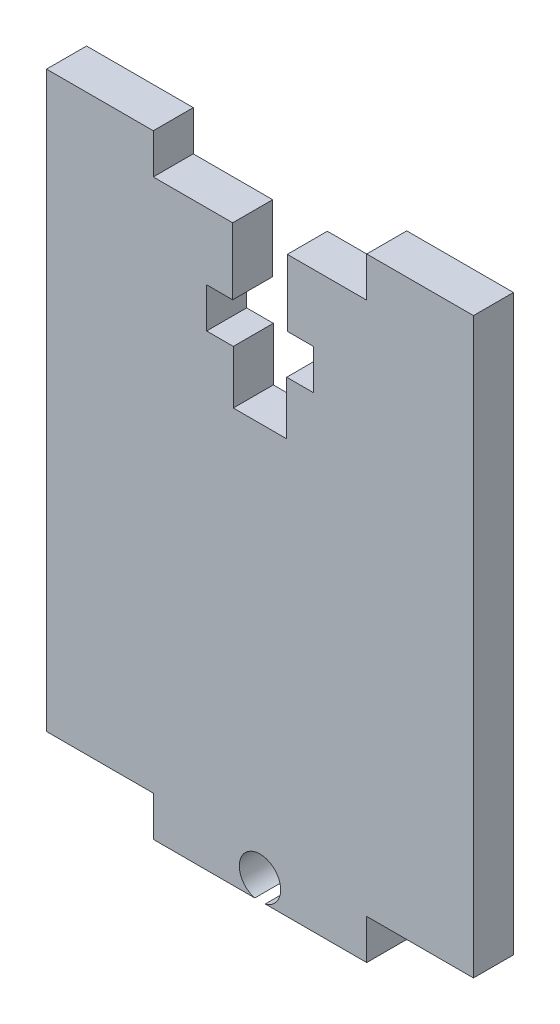
SolidWorks part; units mm, degrees
ref_plane "前视" through (0, 0, 0) normal (0, 0, 1) x (1, 0, 0)
ref_plane "上视" through (0, 0, 0) normal (0, 1, 0) x (1, 0, 0)
ref_plane "右视" through (0, 0, 0) normal (1, 0, 0) x (0, 0, -1)
sketch "草图2" plane through (0, 0, 0) normal (0, 0, 1) x (1, 0, 0)
  line L0 (0, 103.0974) -> (0, -63.3868) construction
  line L1 (2.0479, 48.8553) -> (8, 48.8553)
  line L2 (8, 48.8553) -> (8, 51.8553)
  line L3 (8, 51.8553) -> (16, 51.8553)
  line L4 (16, 51.8553) -> (16, 8.8553)
  line L5 (16, 8.8553) -> (8, 8.8553)
  line L6 (2.0479, 48.8553) -> (2.0479, 43.8553)
  line L7 (2.0479, 43.8553) -> (4, 43.8553)
  line L8 (4, 43.8553) -> (4, 40.8553)
  line L9 (4, 40.8553) -> (2, 40.8553)
  line L10 (2, 40.8553) -> (2, 36.8553)
  line L11 (2, 36.8553) -> (-2, 36.8553)
  line L12 (-8, 5.8553) -> (-0.3905, 5.8553)
  line L13 (8, 5.8553) -> (8, 8.8553)
  line L14 (-8, 5.8553) -> (-8, 8.8553)
  line L15 (0.3905, 5.8553) -> (8, 5.8553)
  line L16 (-2, 40.8553) -> (-2, 36.8553)
  line L17 (-4, 40.8553) -> (-2, 40.8553)
  line L18 (-4, 43.8553) -> (-4, 40.8553)
  line L19 (-2.0479, 43.8553) -> (-4, 43.8553)
  line L20 (-2.0479, 48.8553) -> (-2.0479, 43.8553)
  line L21 (-16, 8.8553) -> (-8, 8.8553)
  line L22 (-16, 51.8553) -> (-16, 8.8553)
  line L23 (-8, 51.8553) -> (-16, 51.8553)
  line L24 (-8, 48.8553) -> (-8, 51.8553)
  line L25 (-2.0479, 48.8553) -> (-8, 48.8553)
  arc A0 (0.3905, 5.8553) -> (-0.3905, 5.8553) centre (0, 7.3553) ccw
  point P22 (0, 36.8553)
  dimension "D12" = 1.5
  dimension "D11" = 3.1
  dimension "D1" = 8
  dimension "D2" = 8
  dimension "D3" = 3
  dimension "D4" = 12
  dimension "D5" = 5
  dimension "D6" = 3
  dimension "D7" = 2
  dimension "D8" = 2
  dimension "D9" = 40
  dimension "D10" = 3
extrude "凸台-拉伸1" add sketch "草图2" along normal blind 3
